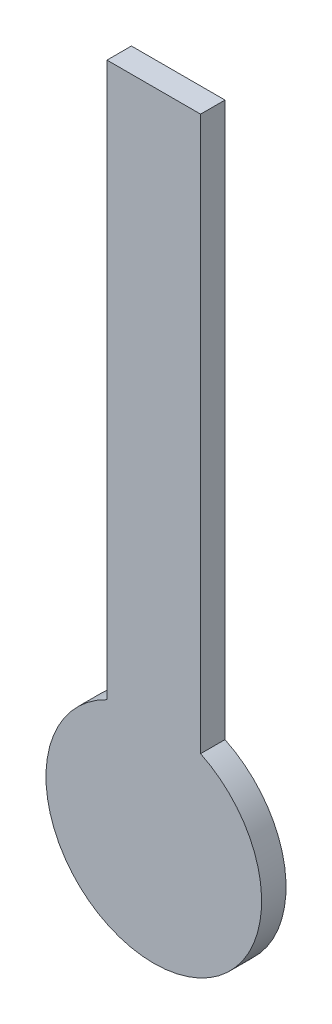
SolidWorks part; units mm, degrees
ref_plane "Front Plane" through (0, 0, 0) normal (0, 0, 1) x (1, 0, 0)
ref_plane "Top Plane" through (0, 0, 0) normal (0, 1, 0) x (1, 0, 0)
ref_plane "Right Plane" through (0, 0, 0) normal (1, 0, 0) x (0, 0, -1)
sketch "Sketch1" plane through (0, 0, 0) normal (0, 0, 1) x (1, 0, 0)
  line L2 (-5.75, 11.9373) -> (-5.75, 80)
  line L3 (-5.75, 80) -> (5.75, 80)
  line L4 (5.75, 11.9373) -> (5.75, 80)
  arc A0 (-5.75, 11.9373) -> (5.75, 11.9373) centre (0, 0) ccw
  point P1 (0, 0)
  point P7 (0, 0)
  point P8 (0, 80)
  dimension "D1" = 26.5
  dimension "D2" = 11.5
  dimension "D3" = 80
extrude "Boss-Extrude1" add sketch "Sketch1" along normal blind 3
